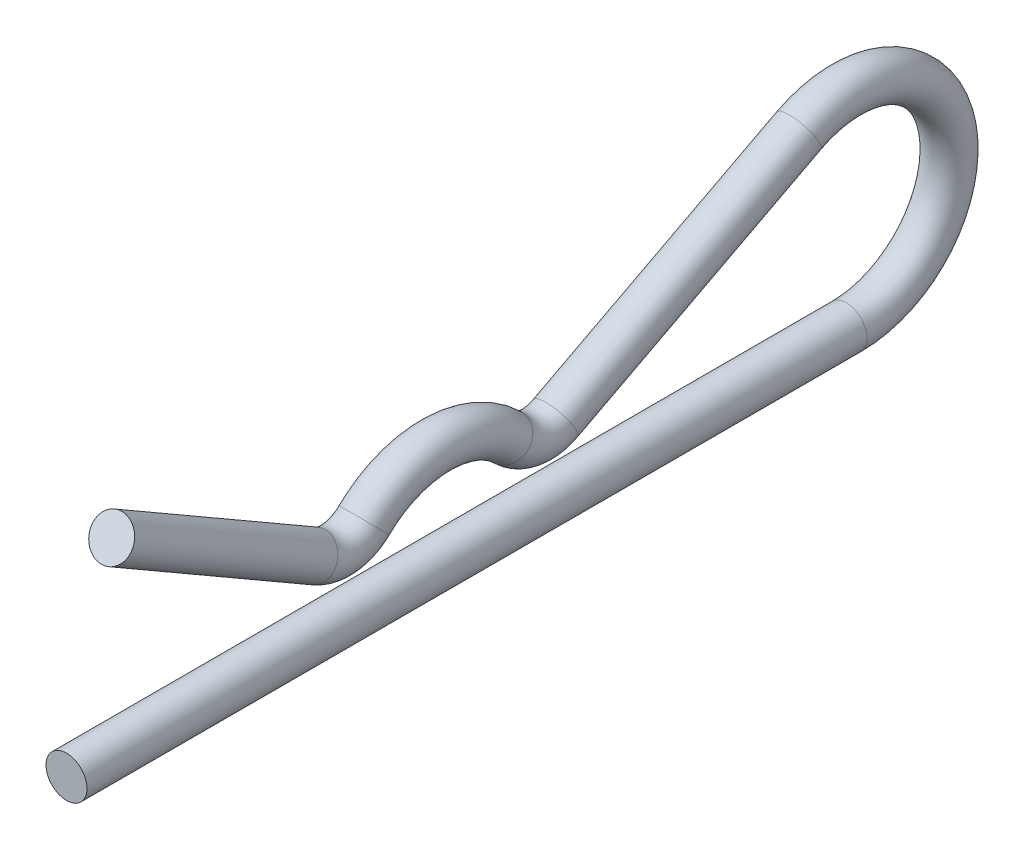
SolidWorks part; units mm, degrees
ref_plane "Front" through (0, 0, 0) normal (0, 0, 1) x (1, 0, 0)
ref_plane "Top" through (0, 0, 0) normal (0, 1, 0) x (1, 0, 0)
ref_plane "Right" through (0, 0, 0) normal (1, 0, 0) x (0, 0, -1)
sketch "Sketch1" plane through (0, 0, 0) normal (0, 0, 1) x (1, 0, 0)
  circle A0 centre (0, 0) radius 0.7937
sketch "Sketch2" plane through (0, 0, 0) normal (1, 0, 0) x (0, 0, -1)
  line L0 (0, 0) -> (30.1625, 0)
  line L1 (10.3989, 3.9687) -> (18.1761, 3.9688) construction
  line L2 (34.925, 0) -> (34.925, 3.9687) construction
  line L3 (34.925, 3.9687) -> (34.1313, 3.9687) construction
  line L5 (34.925, 0) -> (0, 0) construction
  line L6 (9.6052, 2.5939) -> (1.7462, 7.1313)
  line L7 (14.2875, 3.9688) -> (14.2875, 0) construction
  line L13 (28.3228, 7.4854) -> (18.9119, 2.5621)
  circle A0 centre (30.1625, 3.9687) radius 3.175 construction
  arc A1 (17.065, 2.8348) -> (11.51, 2.8348) centre (14.2875, 0) ccw
  arc A6 (11.51, 2.8348) -> (9.6052, 2.5939) centre (10.3989, 3.9687) cw
  arc A8 (18.9119, 2.5621) -> (17.065, 2.8348) centre (18.1761, 3.9688) cw
  arc A9 (30.1625, 0) -> (28.3228, 7.4854) centre (30.1625, 3.9687) ccw
  dimension "D1" = 1.5875
  dimension "D2" = 14.2875
  dimension "D5" = 1.7463
  dimension "D9" = 30
  dimension "D11" = 0.7937
  dimension "D3" = 0.7937
sweep "Sweep1" add profiles "Sketch1" path "Sketch2"
equation "\"D11@Sketch2\" = \"WireOD@Sketch1\"/2"
equation "\"D1@Sketch2\" = \"EyeID@Sketch2\"/4"
equation "\"D3@Sketch2\" = \"D11@Sketch2\""
equation "\"D2@Sketch2\" = (\"Length@Sketch2\"-\"EyeID@Sketch2\")/2"
equation "\"D5@Sketch2\" = \"Length@Sketch2\"*.05"
